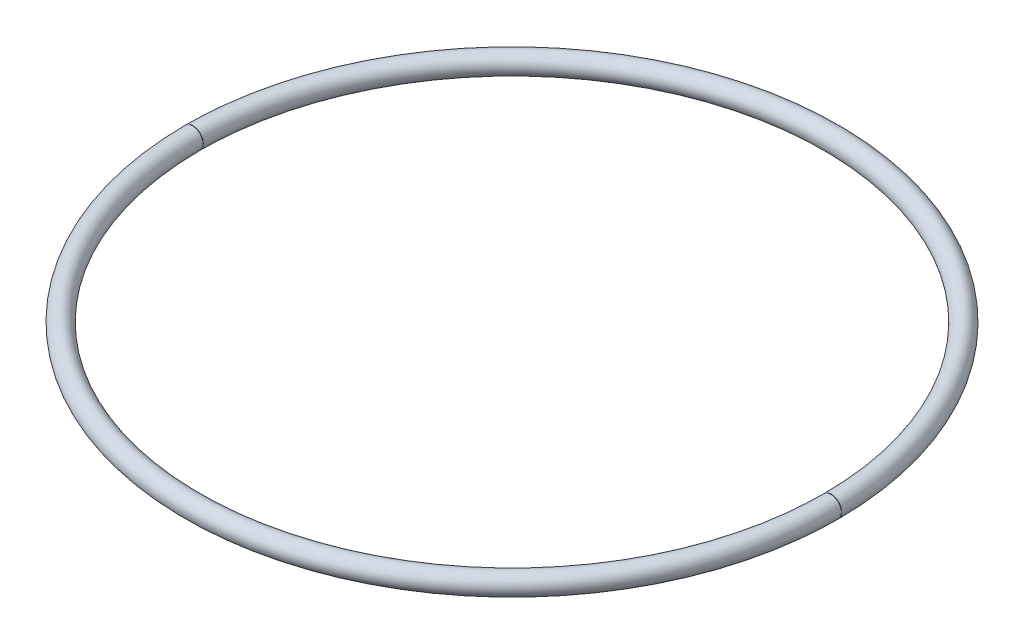
SolidWorks part; units mm, degrees
material "6061 Alloy"
ref_plane "Front Plane" through (0, 0, 0) normal (0, 0, 1) x (1, 0, 0)
ref_plane "Top Plane" through (0, 0, 0) normal (0, 1, 0) x (1, 0, 0)
ref_plane "Right Plane" through (0, 0, 0) normal (1, 0, 0) x (0, 0, -1)
sketch "Sketch1" plane through (0, 0, 0) normal (0, 1, 0) x (1, 0, 0)
  line L1 (758.825, -0.3969) -> (809.625, -0.3969)
  line L2 (758.825, -0.3969) -> (758.825, 0.3969)
  line L3 (758.825, 0.3969) -> (809.625, 0.3969)
  line L4 (809.625, -0.3969) -> (809.625, 0.3969)
  line L5 (758.825, -0.3969) -> (809.625, 0.3969) construction
  line L6 (758.825, 0.3969) -> (809.625, -0.3969) construction
  circle A0 centre (0, 0) radius 784.225
  point P3 (784.225, 0)
  point P8 (809.625, 0)
  dimension "D1" = 1568.45
  dimension "D2" = 50.8
  dimension "D3" = 0.7937
  dimension "D4" = 809.625
sketch "Sketch24" plane through (0, 0, 0) normal (0, 1, 0) x (1, 0, 0)
  line L2 (758.825, 0.3969) -> (809.625, 0.3969) construction
  line L3 (758.825, -0.3969) -> (809.625, -0.3969) construction
  circle A0 centre (0, 0) radius 784.225 construction
  arc A1 (784.2249, 0.3969) -> (784.2249, -0.3969) centre (0, 0) ccw
sweep "Sweep2" add path "Sketch24" circular profile diameter 50.8 parameters "D3"=50.8
shell "Shell1" thickness 3.175
sketch "Sketch25" plane through (0, 0, 0) normal (0, 1, 0) x (1, 0, 0)
  line L0 (758.8249, 0.384) -> (809.6249, 0.4097) construction
  line L1 (-825.5, 0.3663) -> (-723.9, 0.3663)
  line L2 (-825.5, 0.3663) -> (-825.5, -0.3663)
  line L3 (-825.5, -0.3663) -> (-723.9, -0.3663)
  line L4 (-723.9, 0.3663) -> (-723.9, -0.3663)
  line L5 (-774.7, -0.3663) -> (-774.7, 0.3663) construction
  line L6 (-825.5, 0) -> (-723.9, 0) construction
  point P0 (-774.7, 0)
  dimension "D1" = 101.6
  dimension "30" = 723.9
extrude "Cut-Extrude1" cut sketch "Sketch25" against normal through all both and the other way through all
